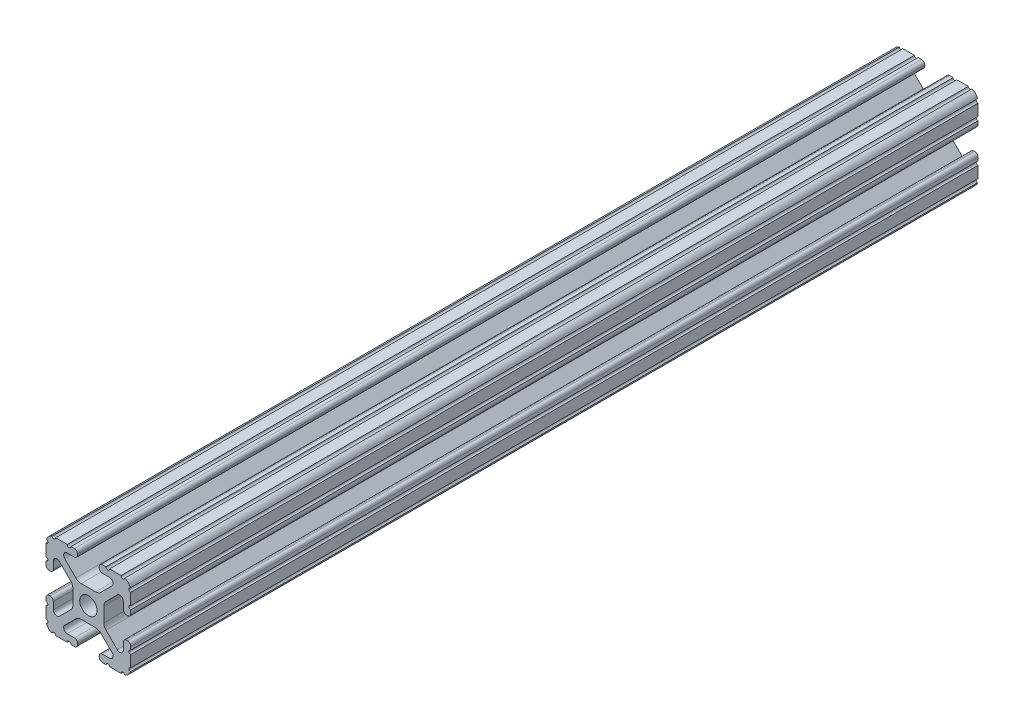
SolidWorks part; units mm, degrees
material "6061-T6 (SS)"
ref_plane "Front Plane" through (0, 0, 0) normal (0, 0, 1) x (1, 0, 0)
ref_plane "Top Plane" through (0, 0, 0) normal (0, 1, 0) x (1, 0, 0)
ref_plane "Right Plane" through (0, 0, 0) normal (1, 0, 0) x (0, 0, -1)
sketch "Sketch2" plane through (0, 0, 0) normal (0, 0, 1) x (1, 0, 0)
  line L0 (0, 12.7) -> (0, -12.7) construction
  line L1 (-12.7, 0) -> (12.7, 0) construction
  line L2 (3.2512, -12.7) -> (12.7, -12.7)
  line L3 (12.7, -12.7) -> (12.7, -3.2512)
  line L4 (3.2512, -12.7) -> (3.2512, -10.4902)
  line L5 (3.2512, -10.4902) -> (8.9276, -10.4902)
  line L6 (8.9276, -10.4902) -> (3.0856, -4.6482)
  line L7 (0, 0) -> (12.7, -12.7) construction
  line L8 (12.7, -3.2512) -> (10.4902, -3.2512)
  line L9 (10.4902, -3.2512) -> (10.4902, -8.9276)
  line L10 (10.4902, -8.9276) -> (4.6482, -3.0856)
  circle A0 centre (0, 0) radius 2.6035
  arc A1 (6.3485, -10.4902) -> (7.1039, -8.6665) centre (6.3485, -9.4219) ccw construction
  point P8 (0, -4.6482)
  dimension "Center Hole Diameter" = 5.207
  dimension "Rail Height" = 25.4
  dimension "Rail Width" = 25.4
  dimension "T-Slot Width" = 6.5024
  dimension "Slot Inner Width" = 14.8336
  dimension "Thickness" = 2.2098
  dimension "Slot Depth" = 5.842
  dimension "D1" = 2.2098
sketch "Sketch3" plane through (0, 0, 0) normal (1, 0, 0) x (0, 0, -1)
  line L0 (-127, -12.7) -> (127, -12.7) construction
  line L1 (-114.3, 0) -> (114.3, 0) construction
  dimension "Length" = 254
  dimension "D1" = 228.6
sketch "Sketch4" plane through (0, 0, 0) normal (0, 0, 1) x (1, 0, 0)
  line L0 (4.1904, -12.7) -> (10.1173, -12.7)
  line L1 (3.2512, -12.7) -> (12.7, -12.7) construction
  line L2 (3.2512, -12.7) -> (3.2512, -10.4902) construction
  line L3 (3.2512, -10.4902) -> (8.9276, -10.4902) construction
  line L4 (3.2512, -11.4294) -> (3.2512, -11.7608)
  line L5 (4.1904, -10.4902) -> (6.3485, -10.4902)
  line L6 (0, -4.6482) -> (2.164, -4.6482)
  line L7 (8.9276, -10.4902) -> (3.0856, -4.6482) construction
  line L8 (3.7373, -5.2999) -> (7.1039, -8.6665)
  line L9 (12.7, -12.7) -> (12.7, -3.2512) construction
  line L10 (10.4902, -8.9276) -> (4.6482, -3.0856) construction
  line L11 (10.4902, -3.2512) -> (10.4902, -8.9276) construction
  line L12 (10.4902, -6.3485) -> (10.4902, -4.1904)
  line L13 (12.7, -3.2512) -> (10.4902, -3.2512) construction
  line L14 (11.4294, -3.2512) -> (11.7608, -3.2512)
  line L15 (12.7, -4.1904) -> (12.7, -10.1173)
  line L16 (8.6665, -7.1039) -> (5.2999, -3.7373)
  line L17 (4.6482, 0) -> (4.6482, -2.164)
  line L18 (-12.7, 0) -> (12.7, 0) construction
  line L19 (0, -4.6482) -> (0, -2.6035)
  line L20 (0, 12.7) -> (0, -12.7) construction
  line L21 (4.6482, 0) -> (2.6035, 0)
  arc A0 (3.2512, -11.7608) -> (4.1904, -12.7) centre (4.1904, -11.7608) ccw
  arc A2 (3.2512, -11.4294) -> (4.1904, -10.4902) centre (4.1904, -11.4294) cw
  arc A3 (6.3485, -10.4902) -> (7.1039, -8.6665) centre (6.3485, -9.4219) ccw
  arc A4 (2.164, -4.6482) -> (3.7373, -5.2999) centre (2.164, -6.8732) cw
  arc A5 (10.1173, -12.7) -> (12.7, -10.1173) centre (10.1173, -10.1173) ccw
  arc A6 (8.6665, -7.1039) -> (10.4902, -6.3485) centre (9.4219, -6.3485) ccw
  arc A7 (10.4902, -4.1904) -> (11.4294, -3.2512) centre (11.4294, -4.1904) cw
  arc A8 (11.7608, -3.2512) -> (12.7, -4.1904) centre (11.7608, -4.1904) cw
  arc A9 (5.2999, -3.7373) -> (4.6482, -2.164) centre (6.8732, -2.164) cw
  circle A10 centre (0, 0) radius 2.6035 construction
  arc A11 (0, -2.6035) -> (2.6035, 0) centre (0, 0) ccw
  dimension "D1" = 2.5827
  dimension "D2" = 2.225
  dimension "D3" = 0.9392
extrude "Boss-Extrude1" add sketch "Sketch4" along normal mid plane 254
sketch "Sketch5" plane through (0, 0, 0) normal (0, 0, 1) x (1, 0, 0)
  line L0 (3.2512, -12.7) -> (12.7, -12.7) construction
  line L1 (4.1904, -10.4902) -> (6.3485, -10.4902) construction
  line L3 (0, 0) -> (12.7, -12.7) construction
  line L4 (6.3485, -10.4902) -> (6.3485, -12.7) construction
  line L5 (8.9276, -10.4902) -> (3.0856, -4.6482) construction
  circle A0 centre (10.3562, -12.7) radius 0.5524
  circle A1 centre (5.796, -12.7) radius 0.5524
  circle A2 centre (12.7, -10.3562) radius 0.5524
  circle A3 centre (12.7, -5.796) radius 0.5524
  point P10 (5.2694, -10.4902)
  point P12 (9.4219, -6.3485)
  dimension "D1" = 1.1049
extrude "Cut-Extrude1" cut sketch "Sketch5" against normal through all both and the other way through all
mirror "Mirror1" about plane through (0, 0, 0) normal (1, 0, 0) of bodies 137 134
mirror "Mirror2" about plane through (0, 0, 0) normal (0, 1, 0) of bodies 135
equation "\"D1@Boss-Extrude1\"=\"Length@Sketch3\""
equation "\"D1@Sketch2\"=\"Thickness@Sketch2\""
equation "\"D2@Sketch4\"=\"Slot Inner Width@Sketch2\"*0.15"
equation "\"D1@Sketch4\"=\"D3@Sketch4\"*2.75"
equation "\"D3@Sketch4\"=\"Thickness@Sketch2\"*0.425"
equation "\"D1@Sketch5\"=\"Thickness@Sketch2\"*0.5"
equation "\"D1@Sketch3\"=\"Length@Sketch3\"*0.9"
